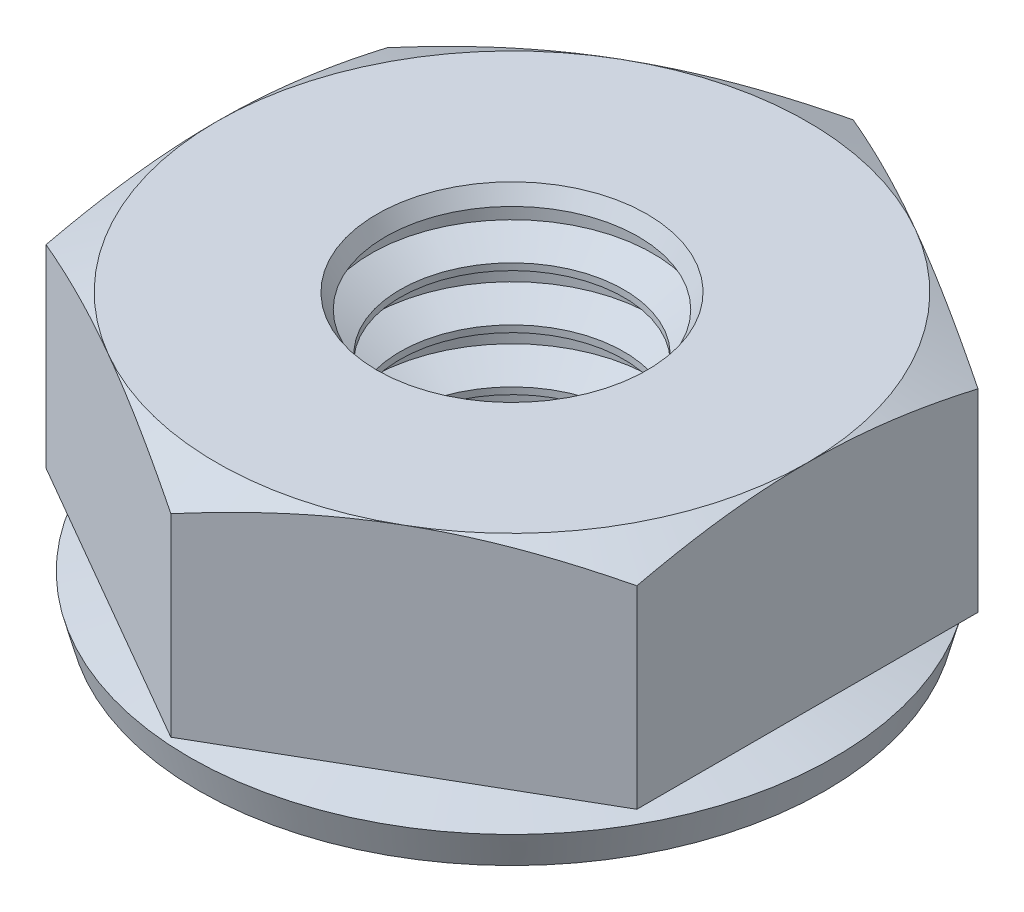
SolidWorks part; units mm, degrees
ref_plane "Front" through (0, 0, 0) normal (0, 0, 1) x (1, 0, 0)
ref_plane "Top" through (0, 0, 0) normal (0, 1, 0) x (1, 0, 0)
ref_plane "Right" through (0, 0, 0) normal (1, 0, 0) x (0, 0, -1)
sketch "Sketch1" plane through (0, 0, 0) normal (0, 1, 0) x (1, 0, 0)
  line L1 (0, 5.041) -> (-4.3656, 2.5205)
  line L2 (-4.3656, 2.5205) -> (-4.3656, -2.5205)
  line L3 (-4.3656, -2.5205) -> (0, -5.041)
  line L4 (0, -5.041) -> (4.3656, -2.5205)
  line L5 (4.3656, -2.5205) -> (4.3656, 2.5205)
  line L6 (4.3656, 2.5205) -> (0, 5.041)
  circle A0 centre (0, 0) radius 4.3656 construction
  dimension "Hex Flats" = 8.7312
extrude "Extrude1" add sketch "Sketch1" along normal mid plane 3.175
sketch "Sketch2" plane through (0, 0, 0) normal (1, 0, 0) x (0, 0, -1)
  line L0 (4.3656, 1.5875) -> (5.041, 1.5875)
  line L1 (5.041, 1.5875) -> (5.041, 1.2726)
  line L2 (5.041, 1.2726) -> (4.3656, 1.5875)
  line L3 (5.041, 1.5875) -> (5.041, -1.5875) construction
  line L4 (2.5205, 1.5875) -> (5.041, 1.5875) construction
  line L5 (0, 1.4214) -> (0, -1.4641) construction
  dimension "D1" = 25
  dimension "D2" = 8.7312
revolve "Cut-Revolve1" cut sketch "Sketch2" angle 360 about L5
sketch "Sketch3" plane through (0, 0, 0) normal (0, 0, 1) x (1, 0, 0)
  line L0 (0, 1.6421) -> (0, -1.6051) construction
  line L1 (1.6532, 1.4883) -> (1.6532, 1.5875)
  line L2 (1.6532, 1.4883) -> (2.0828, 1.2402)
  line L3 (2.0828, 1.2402) -> (2.0828, 1.0418)
  line L4 (2.0828, 1.0418) -> (1.6532, 0.7937)
  line L5 (1.6532, 1.5875) -> (0, 1.5875)
  line L6 (2.0828, 1.141) -> (1.6532, 1.141) construction
  line L8 (0, 1.5875) -> (0, 0.7937)
  line L9 (0, 0.7937) -> (1.6532, 0.7937)
  line L10 (1.6532, 0.7937) -> (1.6532, 1.4883) construction
  line L12 (2.1828, 1.5875) -> (-2.1828, 1.5875) construction
  dimension "D1" = 60
  dimension "D2" = 0.0992
  dimension "Major Dia" = 4.1656
  dimension "D4" = 0.1984
  dimension "Pitch" = 0.7937
revolve "Cut-Revolve3" cut sketch "Sketch3" angle 360 about L0
pattern_linear "LPattern2" count 5 spacing 0.7937 along (0, -1, 0) of "Cut-Revolve3"
sketch "Sketch4" plane through (0, 0, 0) normal (0, 0, 1) x (1, 0, 0)
  line L0 (1.868, 1.3643) -> (1.9969, 1.5875)
  line L1 (2.0828, 1.2402) -> (1.6532, 1.4883) construction
  line L2 (1.9969, 1.5875) -> (1.6532, 1.5875)
  line L3 (1.6532, 1.5875) -> (1.6532, 1.4883)
  line L5 (1.6532, 1.4883) -> (1.868, 1.3643)
  line L9 (1.6532, 1.4883) -> (1.6532, 1.5875) construction
  line L10 (2.1828, 1.5875) -> (-2.1828, 1.5875) construction
  line L11 (0, 1.7859) -> (0, 1.3304) construction
  line L12 (0, 0.248) -> (0, 0) construction
revolve "Cut-Revolve4" cut sketch "Sketch4" angle 360 about L11
sketch "Sketch12" plane through (0, 0, 0) normal (1, 0, 0) x (0, 0, -1)
  line L0 (0, 1.6201) -> (0, -1.5191) construction
  line L1 (2.7005, -1.7145) -> (3.7494, -1.7145)
  line L2 (3.7494, -1.7145) -> (4.7625, -1.986)
  line L3 (4.7625, -1.986) -> (4.631, -2.4767)
  line L4 (4.631, -2.4767) -> (3.6179, -2.2052)
  line L5 (3.6179, -2.2052) -> (2.0828, -2.2052)
  line L6 (2.0828, -1.5875) -> (2.0828, -2.2052)
  line L7 (2.0828, 1.0418) -> (2.0828, 1.2402) construction
  line L10 (2.7005, -1.5875) -> (2.7005, -1.7145)
  line L11 (2.7005, -1.5875) -> (2.0828, -1.5875)
  line L12 (-2.5205, -1.5875) -> (2.5205, -1.5875) construction
  line L14 (3.7494, -1.7145) -> (3.6179, -2.2052) construction
  dimension "Washer Dia" = 9.525
  dimension "D2" = 165
  dimension "D3" = 0.508
  dimension "D4" = 0.127
revolve "Revolve1" add sketch "Sketch12" angle 360 about L0
equation "\"D2@Sketch2\" = \"Hex Flats@Sketch1\""
equation "\"D2@Sketch3\" = \"Pitch@Sketch3\"/8"
equation "\"D4@Sketch3\"=\"Pitch@Sketch3\"/4"
equation "\"D3@LPattern2\" = \"Pitch@Sketch3\""
equation "\"D1@LPattern2\"=int(\"Height1@Extrude1\"/\"Pitch@Sketch3\")+1"
